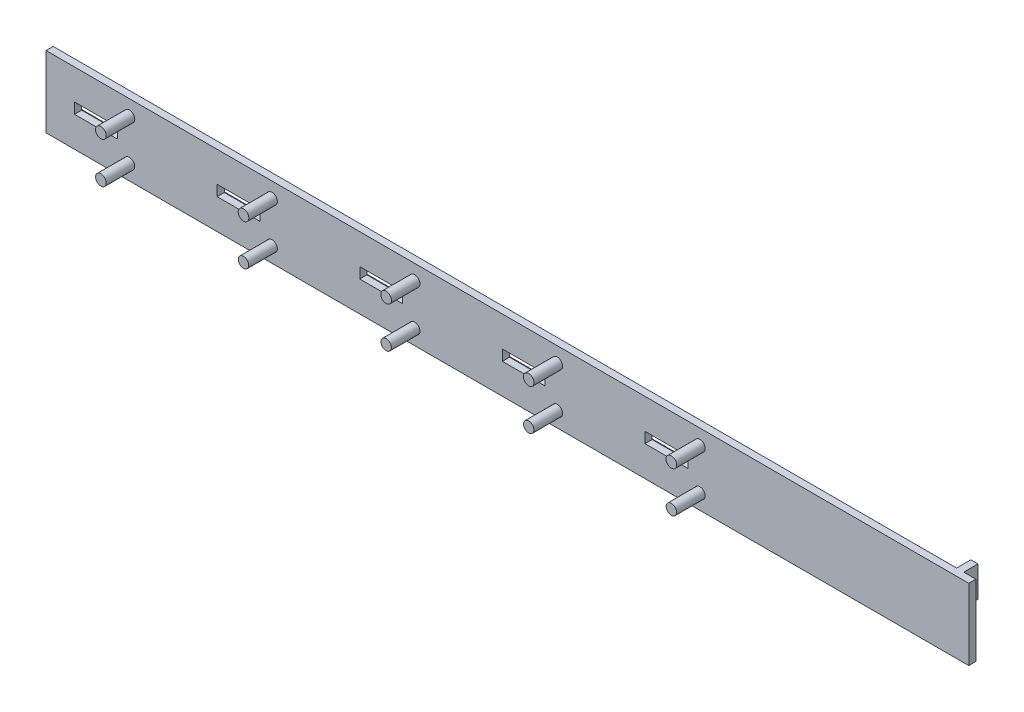
SolidWorks part; units mm, degrees
ref_plane "Front Plane" through (0, 0, 0) normal (0, 0, 1) x (1, 0, 0)
ref_plane "Top Plane" through (0, 0, 0) normal (0, 1, 0) x (1, 0, 0)
ref_plane "Right Plane" through (0, 0, 0) normal (1, 0, 0) x (0, 0, -1)
sketch "Sketch1" plane through (0, 0, 0) normal (0, 0, 1) x (1, 0, 0)
  line L0 (116.9601, 100) -> (116.9601, 78.75) construction
  line L1 (0, 0) -> (1000, 0)
  line L2 (0, 0) -> (0, 100)
  line L3 (0, 100) -> (1000, 100)
  line L5 (40, 57.5) -> (100, 57.5)
  line L6 (40, 57.5) -> (40, 42.5)
  line L7 (40, 42.5) -> (100, 42.5)
  line L8 (100, 57.5) -> (100, 42.5)
  line L9 (0, 50) -> (1485.7922, 50) construction
  line L10 (116.9601, 0) -> (116.9601, 21.25) construction
  line L11 (240, 42.5) -> (300, 42.5)
  line L12 (240, 57.5) -> (240, 42.5)
  line L13 (240, 57.5) -> (300, 57.5)
  line L14 (300, 57.5) -> (300, 42.5)
  line L15 (440, 42.5) -> (500, 42.5)
  line L16 (440, 57.5) -> (440, 42.5)
  line L17 (440, 57.5) -> (500, 57.5)
  line L18 (500, 57.5) -> (500, 42.5)
  line L19 (640, 42.5) -> (700, 42.5)
  line L20 (640, 57.5) -> (640, 42.5)
  line L21 (640, 57.5) -> (700, 57.5)
  line L22 (700, 57.5) -> (700, 42.5)
  line L23 (840, 42.5) -> (900, 42.5)
  line L24 (840, 57.5) -> (840, 42.5)
  line L25 (840, 57.5) -> (900, 57.5)
  line L26 (900, 57.5) -> (900, 42.5)
  line L28 (1000, 100) -> (1294.0475, 100)
  line L30 (1000, 0) -> (1294.0475, 0)
  line L31 (1294.0475, 100) -> (1294.0475, 0)
  circle A1 centre (116.9601, 78.75) radius 7.5
  circle A2 centre (116.9601, 21.25) radius 7.5
  circle A3 centre (316.9601, 78.75) radius 7.5
  circle A4 centre (316.9601, 21.25) radius 7.5
  circle A5 centre (516.9601, 78.75) radius 7.5
  circle A6 centre (516.9601, 21.25) radius 7.5
  circle A7 centre (716.9601, 78.75) radius 7.5
  circle A8 centre (716.9601, 21.25) radius 7.5
  circle A9 centre (916.9601, 78.75) radius 7.5
  circle A10 centre (916.9601, 21.25) radius 7.5
  point P9 (40, 50)
  dimension "D9" = 15
  dimension "D1" = 1000
  dimension "D2" = 100
  dimension "D3" = 60
  dimension "D4" = 15
  dimension "D5" = 40
  dimension "D6" = 42.5
  dimension "D7" = 21.25
  dimension "D8" = 21.25
  dimension "D10" = 5
extrude "Boss-Extrude1" add sketch "Sketch1" along normal blind 10
sketch "Sketch3" plane through (0, 0, 0) normal (0, 0, 1) x (1, 0, 0)
  circle A0 centre (116.9601, 78.75) radius 7.5
  circle A1 centre (116.9601, 21.25) radius 7.5
  circle A2 centre (316.9601, 78.75) radius 7.5
  circle A3 centre (316.9601, 21.25) radius 7.3026
  circle A4 centre (516.9601, 21.25) radius 7.3026
  circle A5 centre (516.9601, 78.75) radius 7.5
  circle A6 centre (716.9601, 21.25) radius 7.3026
  circle A7 centre (716.9601, 78.75) radius 7.5
  circle A8 centre (916.9601, 21.25) radius 7.3026
  circle A9 centre (916.9601, 78.75) radius 7.5
  dimension "D1" = 4
extrude "Boss-Extrude3" add sketch "Sketch3" along normal blind 50
sketch "Sketch6" plane through (0, 0, 0) normal (0, 0, -1) x (-1, 0, 0)
  line L0 (-900, 57.5) -> (-900, 61.5)
  line L1 (-900, 42.5) -> (-900, 38.5)
  line L2 (0, 100) -> (0, 0) construction
  line L3 (-900, 61.5) -> (0, 61.5)
  line L4 (-900, 61.5) -> (-900, 65.5)
  line L5 (-900, 65.5) -> (0, 65.5)
  line L6 (0, 61.5) -> (0, 65.5)
  line L8 (-900, 38.5) -> (0, 38.5)
  line L9 (-900, 38.5) -> (-900, 34.5)
  line L10 (-900, 34.5) -> (0, 34.5)
  line L11 (0, 38.5) -> (0, 34.5)
  dimension "D1" = 4
  dimension "D2" = 4
  dimension "D3" = 4
extrude "Boss-Extrude6" add sketch "Sketch6" along normal blind 5 contours L3 L6 L5 L4 | L9 L10 L11 L8
sketch "Sketch7" plane through (0, 0, 0) normal (0, 0, 1) x (1, 0, 0)
  line L0 (1276.9868, 100) -> (1276.9868, 57)
  line L2 (1294.0475, 100) -> (0, 100) construction
  line L3 (1276.9868, 57) -> (1266.9868, 57)
  line L4 (1266.9868, 57) -> (1266.9868, 100)
  line L5 (1266.9868, 100) -> (1276.9868, 100)
  line L6 (0, 0) -> (1294.0475, 0) construction
  line L7 (1260.6779, 0) -> (1250.6779, 0)
  line L8 (1260.6779, 0) -> (1260.6779, 45)
  line L9 (1260.6779, 45) -> (1250.6779, 45)
  line L10 (1250.6779, 0) -> (1250.6779, 45)
  dimension "D1" = 10
  dimension "D2" = 43
  dimension "D3" = 10
  dimension "D4" = 45
extrude "Boss-Extrude7" add sketch "Sketch7" against normal blind 20
sketch "Sketch9" plane through (1260.6779, 0, 0) normal (1, 0, 0) x (0, 0, -1)
  arc A0 (0, 45) -> (20, 45) centre (10, 49.4599) ccw
extrude "Cut-Extrude1" cut sketch "Sketch9" against normal blind 20 and the other way through all
